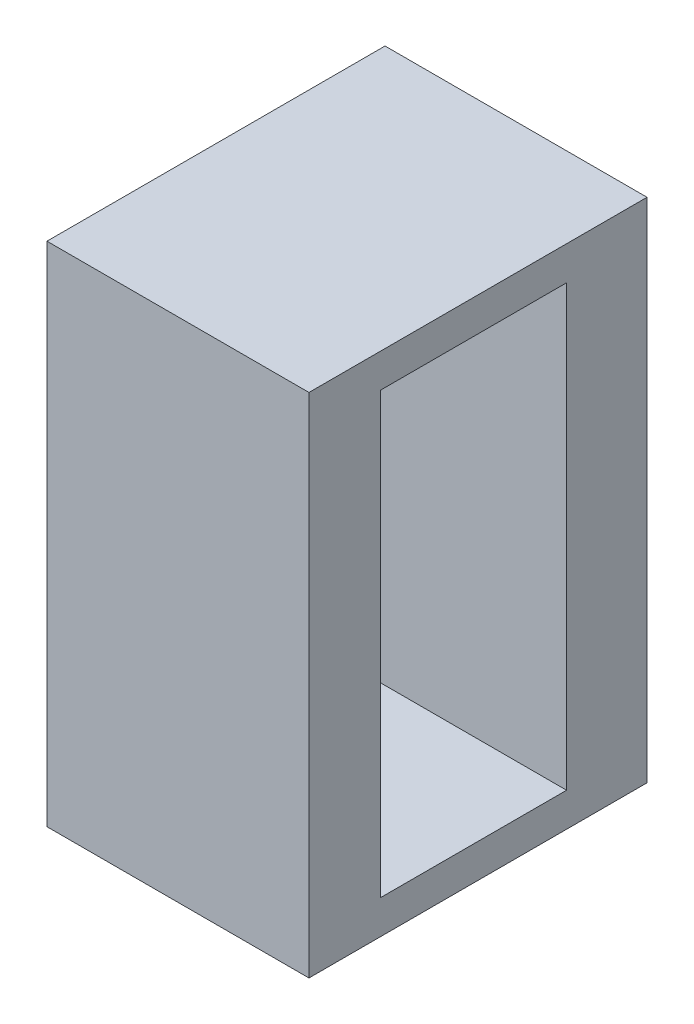
SolidWorks part; units mm, degrees
ref_plane "前视基准面" through (0, 0, 0) normal (0, 0, 1) x (1, 0, 0)
ref_plane "上视基准面" through (0, 0, 0) normal (0, 1, 0) x (1, 0, 0)
ref_plane "右视基准面" through (0, 0, 0) normal (1, 0, 0) x (0, 0, -1)
other "Configuration Table"
sketch "草图1" plane through (0, 0, 0) normal (0, 0, 1) x (1, 0, 0)
  line L1 (-3.8803, 20.8834) -> (-0.7803, 20.8834)
  line L2 (-3.8803, 20.8834) -> (-3.8803, 14.8834)
  line L3 (-3.8803, 14.8834) -> (-0.7803, 14.8834)
  line L4 (-0.7803, 20.8834) -> (-0.7803, 14.8834)
extrude "凸台-拉伸1" add sketch "草图1" along normal blind 4 contours L2 L3 L4 L1
sketch "草图2" plane through (-0.7803, 0, 0) normal (1, 0, 0) x (0, 0, -1)
  line L1 (-3.152, 20.4834) -> (-0.952, 20.4834)
  line L2 (-3.152, 20.4834) -> (-3.152, 15.2834)
  line L3 (-3.152, 15.2834) -> (-0.952, 15.2834)
  line L4 (-0.952, 20.4834) -> (-0.952, 15.2834)
  line L5 (-4, 17.8834) -> (-0.2632, 17.8834) construction
  line L6 (-4, 20.8834) -> (-4, 14.8834) construction
  dimension "D1" = 2.2
  dimension "D2" = 5.2
extrude "切除-拉伸1" cut sketch "草图2" against normal blind 2.7
